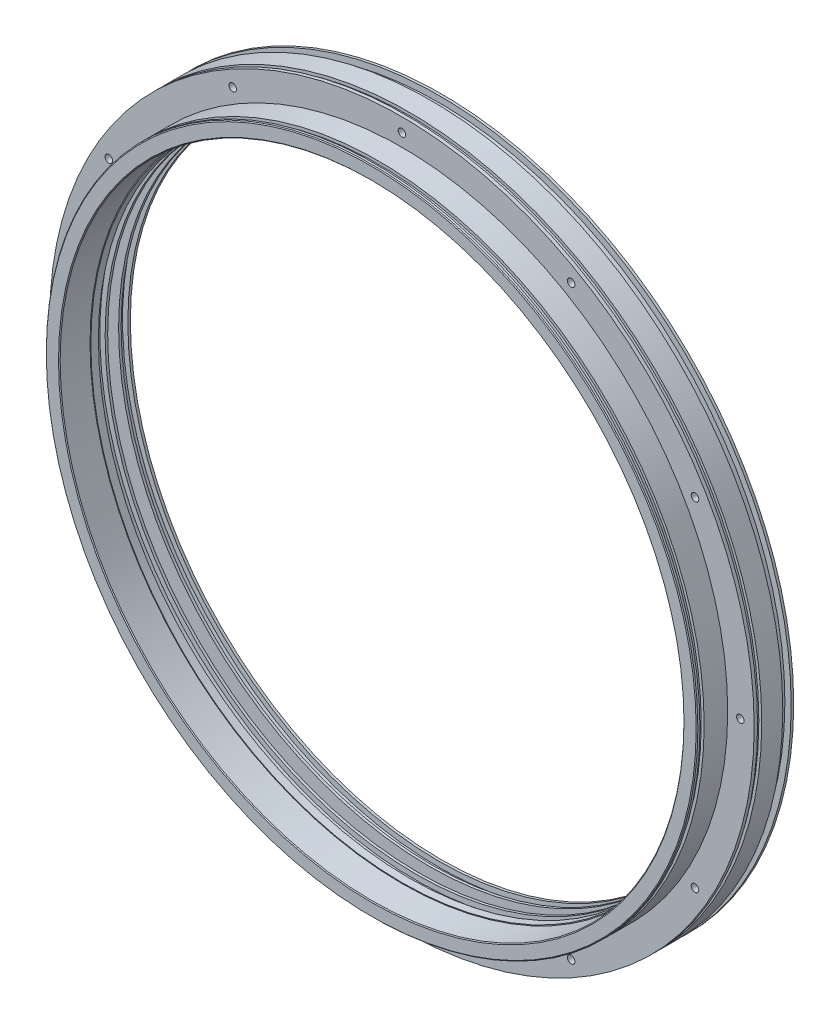
SolidWorks part; units mm, degrees
material "1.4401 (X5CrNiMo17-12-2)"
ref_plane "Ebene vorne" through (0, 0, 0) normal (0, 0, 1) x (1, 0, 0)
ref_plane "Ebene oben" through (0, 0, 0) normal (0, 1, 0) x (1, 0, 0)
ref_plane "Ebene rechts" through (0, 0, 0) normal (1, 0, 0) x (0, 0, -1)
sketch "Skizze1" plane through (0, 0, 0) normal (1, 0, 0) x (0, 0, -1)
  line L0 (0, 0) -> (50000, 0) construction
  line L1 (0, 371) -> (0, 387.5)
  line L2 (0, 387.5) -> (3.5, 387.5)
  line L3 (3.5, 387.5) -> (3.5, 384)
  line L4 (3.5, 384) -> (8.5, 384)
  line L5 (8.5, 384) -> (8.5, 387.5)
  line L6 (8.5, 387.5) -> (36.5, 387.5)
  line L7 (36.5, 387.5) -> (36.5, 419)
  line L8 (36.5, 419) -> (40.5, 419)
  line L9 (40.5, 419) -> (40.5, 415.5)
  line L10 (40.5, 415.5) -> (45.5, 415.5)
  line L11 (45.5, 415.5) -> (45.5, 419)
  line L12 (45.5, 419) -> (70.5, 419)
  line L13 (70.5, 419) -> (70.5, 411.5)
  line L14 (70.5, 411.5) -> (80.5, 411.5)
  line L15 (80.5, 411.5) -> (80.5, 419)
  line L16 (80.5, 419) -> (83.5, 419)
  line L17 (83.5, 419) -> (83.5, 370)
  line L18 (83.5, 370) -> (80.5, 370)
  line L19 (80.5, 370) -> (80.5, 376.3)
  line L20 (80.5, 376.3) -> (72.5, 376.3)
  line L21 (72.5, 376.3) -> (72.5, 370)
  line L22 (72.5, 370) -> (69.5, 370)
  line L23 (69.5, 370) -> (69.5, 393.8)
  line L24 (69.5, 393.8) -> (56.5, 393.8)
  line L25 (56.5, 393.8) -> (56.5, 370)
  line L26 (56.5, 370) -> (53.5, 370)
  line L27 (36.5, 370) -> (36.5, 371)
  line L28 (36.5, 371) -> (0, 371)
  line L29 (53.5, 370) -> (53.5, 376.3)
  line L30 (53.5, 376.3) -> (45.5, 376.3)
  line L31 (45.5, 376.3) -> (45.5, 370)
  line L32 (45.5, 370) -> (36.5, 370)
  dimension "D1" = 5
  dimension "D2" = 3.5
  dimension "D3" = 10
  dimension "D4" = 3
  dimension "D5" = 3
  dimension "D6" = 8
  dimension "D7" = 13
  dimension "D8" = 23.8
  dimension "D9" = 1
  dimension "D10" = 5
  dimension "D11" = 3.5
  dimension "D12" = 75
  dimension "D13" = 14
  dimension "D14" = 8
  dimension "D15" = 6.3
  dimension "D16" = 6.3
  dimension "D17" = 30
  dimension "D18" = 47
  dimension "D19" = 38
  dimension "D20" = 47
  dimension "D21" = 83.5
  dimension "D22" = 419
  dimension "D23" = 387.5
  dimension "D24" = 7.5
  dimension "D25" = 370
revolve "Rotation1" add sketch "Skizze1" angle 360 about L0
chamfer "Fase1" distance 1 angle 45 2 edges at (387.5, 0, 0) (371, 0, 0)
sketch "Skizze2" plane through (0, 0, -83.5) normal (0, 0, -1) x (-1, 0, 0)
  line L0 (0, 0) -> (0, 402.5) construction
  dimension "D1" = 402.5
hole_wizard "Bohrung1" positions "Skizze4" profile "Skizze3" legacy end condition through all
sketch "Skizze4" plane through (0, 0, -83.5) normal (0, 0, -1) x (-1, 0, 0)
  point P0 (0, 402.5)
sketch "Skizze3" plane through (0, 402.5, -83.5) normal (1, 0, 0) x (0, 1, 0)
  line L0 (0, 0) -> (0, 86.2039)
  line L1 (0, 86.2039) -> (4.5, 83.5)
  line L2 (4.5, 83.5) -> (4.5, 9)
  line L3 (4.5, 9) -> (7.5, 9)
  line L4 (7.5, 0) -> (0, 0)
  line L5 (0, -11.3109) -> (0, 121.1557) construction
  line L6 (0, 86.2039) -> (-4.5, 83.5) construction
  line L7 (7.5, 9) -> (7.5, 0)
  dimension "Durchmesser" = 9
  dimension "Tiefe" = 83.5
  dimension "Senkdurchmesser3" = 15
  dimension "Senktiefe1" = 9
  dimension "Spitzenwinkel" = 118
pattern_circular "Kreismuster1" count 12 over 360 about axis through (0, 0, 0) along (0, 0, 1) of "Bohrung1"
